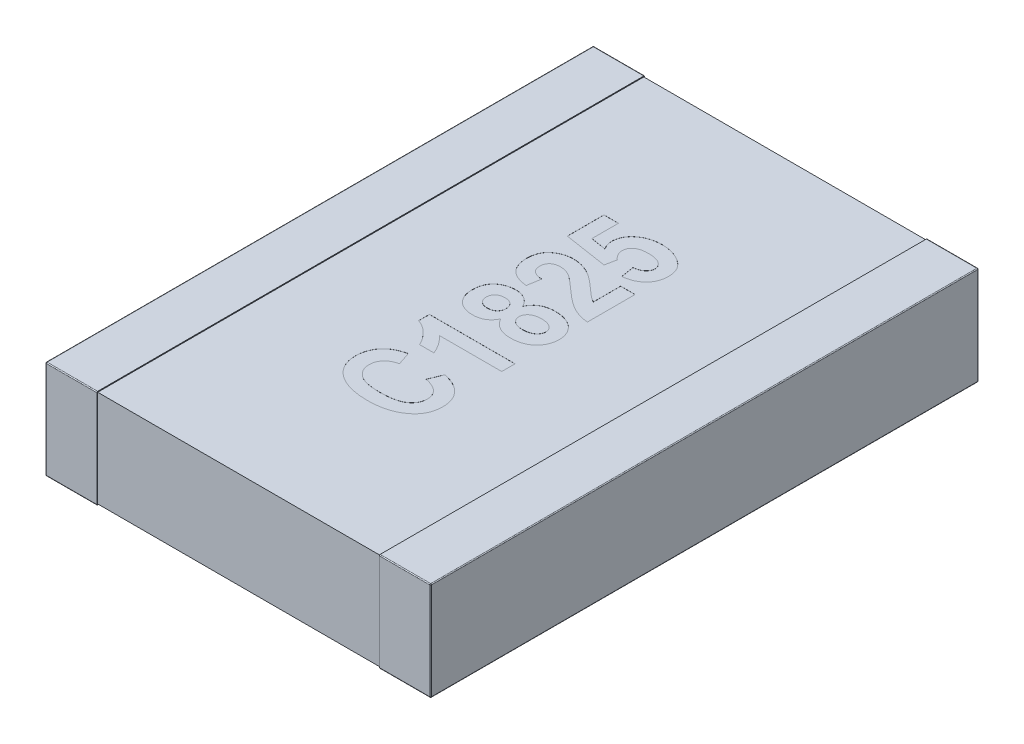
SolidWorks part; units mm, degrees
ref_plane "Front Plane" through (0, 0, 0) normal (0, 0, 1) x (1, 0, 0)
ref_plane "Top Plane" through (0, 0, 0) normal (0, 1, 0) x (1, 0, 0)
ref_plane "Right Plane" through (0, 0, 0) normal (1, 0, 0) x (0, 0, -1)
sketch "Sketch1" plane through (0, 0, 0) normal (0, 1, 0) x (1, 0, 0)
  line L0 (0, 0.15) -> (0, -0.15) construction
  line L1 (-2.25, 0) -> (0, 0) construction
  line L3 (-2.25, 3.2) -> (-1.65, 3.2)
  line L4 (-2.25, 3.2) -> (-2.25, -3.2)
  line L5 (-2.25, -3.2) -> (-1.65, -3.2)
  line L6 (-1.65, 3.2) -> (-1.65, -3.2)
  dimension "BANDWIDTH" = 0.6
  dimension "WIDTH" = 6.4
  dimension "LENGTH-HALF" = 2.25
extrude "THICKNESS" add sketch "Sketch1" along normal blind 1.15
fillet "Fillet1" radius 0.01 8 edges at (-2.25, 0, 0) (-1.95, 0, -3.2) (-2.25, 0.575, -3.2) (-1.95, 0, 3.2) (-2.25, 0.575, 3.2) (-2.25, 1.15, 0) (-1.95, 1.15, -3.2) (-1.95, 1.15, 3.2)
sketch "Sketch2" plane through (0, 0, 0) normal (1, 0, 0) x (0, 0, -1)
  line L0 (0, 1.15) -> (0, 0) construction
  line L1 (-3.19, 1.14) -> (3.19, 1.14)
  line L2 (-3.19, 1.14) -> (-3.19, 0.01)
  line L3 (-3.19, 0.01) -> (3.19, 0.01)
  line L4 (3.19, 1.14) -> (3.19, 0.01)
  line L5 (-3.19, 1.15) -> (3.19, 1.15) construction
  line L6 (-3.19, 0) -> (3.19, 0) construction
  line L7 (-3.2, 0.575) -> (3.2, 0.575) construction
  line L8 (-3.2, 1.14) -> (-3.2, 0.01) construction
  line L9 (3.2, 1.14) -> (3.2, 0.01) construction
  dimension "D1" = 0.01
  dimension "D2" = 0.01
extrude "Boss-Extrude2" add sketch "Sketch2" against normal up to surface (1.65 mm away) up to face at (-1.65, 0.575, 0)
mirror "Mirror3" about plane through (0, 0, 0) normal (1, 0, 0) of "Boss-Extrude2", "Fillet1", "THICKNESS"
sketch "Sketch3" plane through (0, 1.14, 0) normal (0, 1, 0) x (1, 0, 0)
  line L0 (0.5, -1.75) -> (0.5, 1.75) construction
  line L1 (-0.6325, 0) -> (0.6325, 0) construction
  line L2 (0, -0.6325) -> (0, 0.6325) construction
  text T0 "<b>C1825</b>" font "Arial Narrow" height 1
  point P2 (0.5, 0)
  dimension "D1" = 0.5
  dimension "D2" = 3.5
extrude "Cut-Extrude1" cut sketch "Sketch3" against normal blind 0.001
